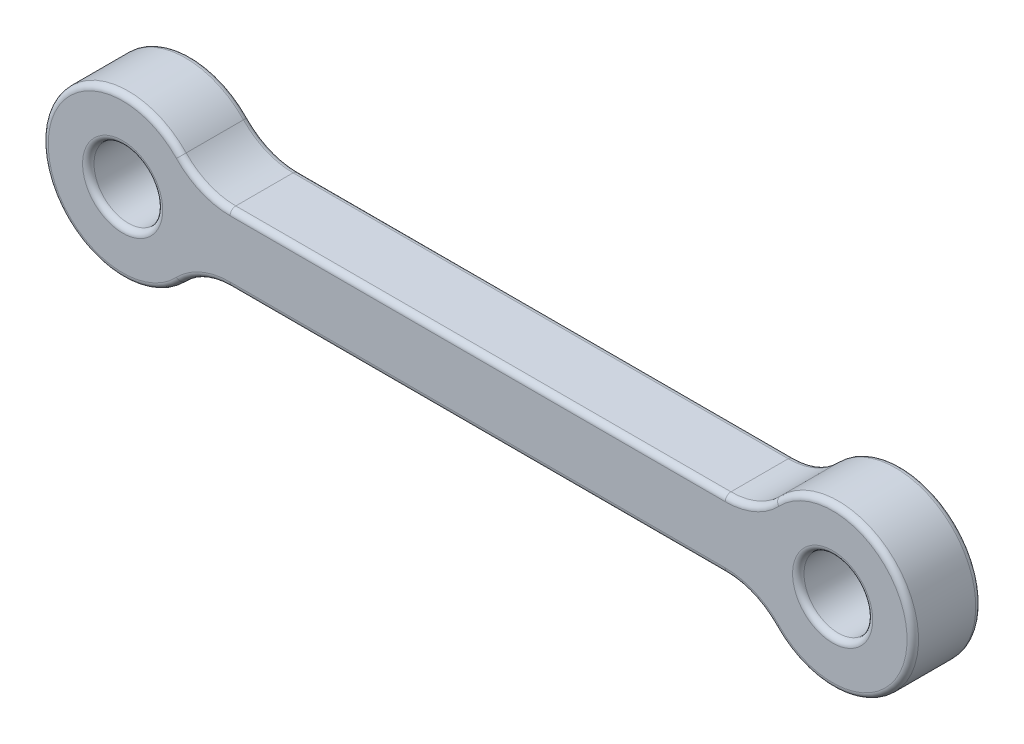
SolidWorks part; units mm, degrees
ref_plane "Front Plane" through (0, 0, 0) normal (0, 0, 1) x (1, 0, 0)
ref_plane "Top Plane" through (0, 0, 0) normal (0, 1, 0) x (1, 0, 0)
ref_plane "Right Plane" through (0, 0, 0) normal (1, 0, 0) x (0, 0, -1)
sketch "Sketch1" plane through (0, 0, 0) normal (0, 0, 1) x (1, 0, 0)
  line L0 (0, 0) -> (31, 0) construction
  line L1 (0, 3.5) -> (31, 3.5) construction
  line L2 (0, -3.5) -> (31, -3.5) construction
  line L3 (15.5, 0) -> (15.5, -3.5) construction
  line L5 (27.8377, -1.5) -> (3.1623, -1.5)
  line L6 (27.8377, -1.5) -> (27.8377, 1.5) construction
  line L7 (27.8377, 1.5) -> (3.1623, 1.5)
  line L8 (3.1623, -1.5) -> (3.1623, 1.5) construction
  line L9 (27.8377, -1.5) -> (3.1623, 1.5) construction
  line L10 (27.8377, 1.5) -> (3.1623, -1.5) construction
  arc A0 (0, 3.5) -> (0, -3.5) centre (0, 0) ccw construction
  arc A1 (31, -3.5) -> (31, 3.5) centre (31, 0) ccw construction
  circle A2 centre (0, 0) radius 1.5
  circle A3 centre (0, 0) radius 3.5
  circle A4 centre (31, 0) radius 3.5
  circle A5 centre (31, 0) radius 1.5
  point P3 (15.5, 0)
  dimension "D3" = 3
  dimension "D1" = 31
  dimension "D2" = 7
  dimension "D4" = 3
extrude "Boss-Extrude1" add sketch "Sketch1" along normal mid plane 3 contours A3 A2 | A4 A5 | L5 A4 L7 A3
fillet "Fillet1" radius 3 4 edges at (27.8377, 1.5, 0) (27.8377, -1.5, 0) (3.1623, -1.5, 0) (3.1623, 1.5, 0)
fillet "Fillet2" radius 0.25 20 edges at (32.5, 0, 1.5) (32.5, 0, -1.5) (27.4863, 1.7404, 1.5) (27.4863, 1.7404, -1.5) (34.5, 0, -1.5) (34.5, 0, 1.5) (27.4863, -1.7404, 1.5) (27.4863, -1.7404, -1.5) (15.5, -1.5, -1.5) (15.5, -1.5, 1.5) (3.5137, -1.7404, 1.5) (3.5137, -1.7404, -1.5) (-3.5, 0, -1.5) (-3.5, 0, 1.5) (3.5137, 1.7404, 1.5) (3.5137, 1.7404, -1.5) (15.5, 1.5, 1.5) (15.5, 1.5, -1.5) (1.5, 0, 1.5) (1.5, 0, -1.5)
